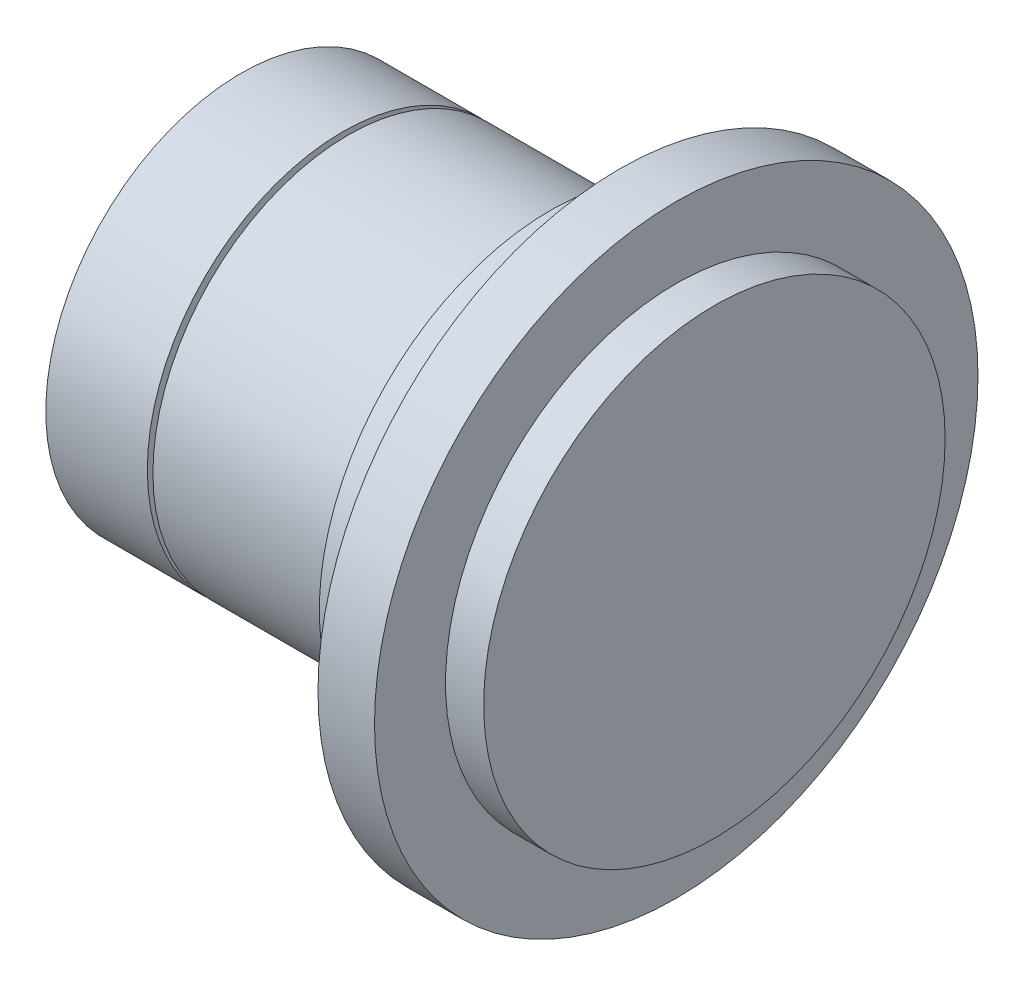
SolidWorks part; units mm, degrees
ref_plane "Přední rovina" through (0, 0, 0) normal (0, 0, 1) x (1, 0, 0)
ref_plane "Vrchní rovina" through (0, 0, 0) normal (0, 1, 0) x (1, 0, 0)
ref_plane "Pravá rovina" through (0, 0, 0) normal (1, 0, 0) x (0, 0, -1)
sketch "Skica1" plane through (0, 0, 0) normal (0, 0, 1) x (1, 0, 0)
  line L0 (0, 0) -> (93.2571, 0)
  line L1 (93.2571, 0) -> (93.2571, 45.4629)
  line L2 (93.2571, 45.4629) -> (85.7448, 45.4629)
  line L3 (85.7448, 45.4629) -> (85.7448, 59.4514)
  line L4 (85.7448, 59.4514) -> (74.6057, 59.4514)
  line L5 (74.6057, 59.4514) -> (74.6057, 45.4629)
  line L6 (74.6057, 45.4629) -> (60.8762, 45.4629)
  line L7 (60.8762, 45.4629) -> (60.8762, 38.4686)
  line L8 (60.8762, 38.4686) -> (0, 38.4686)
  line L9 (0, 38.4686) -> (0, 0)
  line L10 (0, 0) -> (-50000, 0) construction
revolve "Rotovat1" add sketch "Skica1" angle 360 about L10
ref_plane "Rovina1" through (20, 0, 0) normal (-1, 0, 0) x (0, 0, 1)
sketch "Skica3" plane through (20, 0, 0) normal (-1, 0, 0) x (0, 0, 1)
  circle A0 centre (0, 0) radius 38.4686 construction
  circle A1 centre (0, 0) radius 38.4686
  circle A2 centre (0, 0) radius 6.2
  dimension "d2" = 12.4
extrude "Odebrat vysunutím1" cut sketch "Skica3" against normal blind 1.1
other "POJISTNÝ KROUŽEK - HŘÍDEL<1>"
